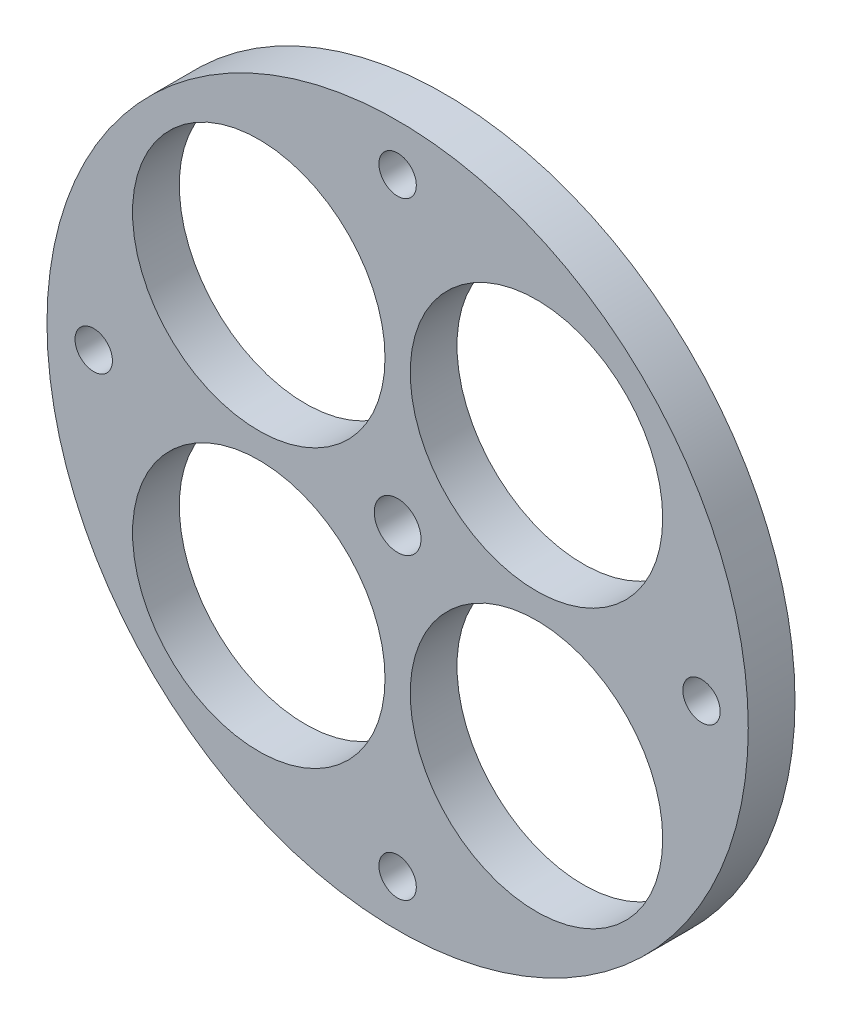
SolidWorks part; units mm, degrees
ref_plane "Front Plane" through (0, 0, 0) normal (0, 0, 1) x (1, 0, 0)
ref_plane "Top Plane" through (0, 0, 0) normal (0, 1, 0) x (1, 0, 0)
ref_plane "Right Plane" through (0, 0, 0) normal (1, 0, 0) x (0, 0, -1)
sketch "Sketch1" plane through (0, 0, 0) normal (0, 0, 1) x (1, 0, 0)
  line L0 (-65, 0) -> (65, 0) construction
  line L1 (0, 65) -> (0, -65) construction
  circle A0 centre (0, 0) radius 75
  circle A1 centre (-29.6985, 29.6985) radius 27
  circle A2 centre (29.6985, 29.6985) radius 27
  circle A3 centre (29.6985, -29.6985) radius 27
  circle A4 centre (-29.6985, -29.6985) radius 27
  circle A5 centre (0, 0) radius 5
  circle A6 centre (0, 0) radius 65 construction
  circle A7 centre (0, 65) radius 4
  circle A8 centre (65, 0) radius 4
  circle A9 centre (0, -65) radius 4
  circle A10 centre (-65, 0) radius 4
  point P15 (0, 0)
  dimension "D1" = 4
extrude "Boss-Extrude1" add sketch "Sketch1" along normal blind 10
